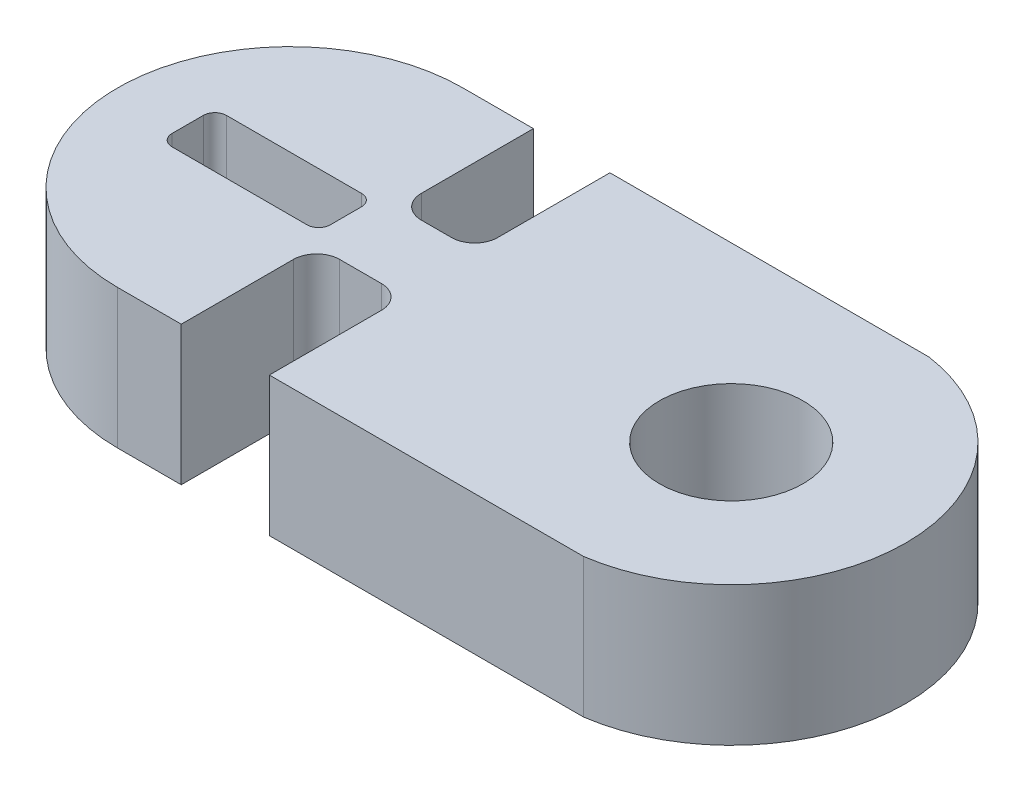
SolidWorks part; units mm, degrees
ref_plane "Alzado" through (0, 0, 0) normal (0, 0, 1) x (1, 0, 0)
ref_plane "Planta" through (0, 0, 0) normal (0, 1, 0) x (1, 0, 0)
ref_plane "Vista lateral" through (0, 0, 0) normal (1, 0, 0) x (0, 0, -1)
sketch "Croquis1" plane through (0, 0, 0) normal (0, 1, 0) x (1, 0, 0)
  line L0 (0, 0) -> (0, 15.4786) construction
  line L1 (0, 0) -> (24.3963, 0) construction
  line L2 (-10.05, 0) -> (8.9725, 0) construction
  line L3 (-10.05, 7.45) -> (-7.01, 7.45)
  line L4 (-10.05, -7.45) -> (-7.3, -7.45)
  line L5 (-17.5, 0) -> (-17.5, -13.5126) construction
  line L6 (16.5, 0) -> (16.5, -12.105) construction
  line L7 (-17.5, -13.5126) -> (-7.3, -13.5126) construction
  line L8 (-3.5, -7.45) -> (10.05, -7.45)
  line L9 (-3.71, 7.45) -> (10.05, 7.45)
  line L10 (-7.3, -7.45) -> (-7.3, -1.6141)
  line L11 (-7.3, -1.6141) -> (-3.5, -1.6141)
  line L12 (-3.5, -7.45) -> (-3.5, -1.6141)
  line L14 (-7.01, 7.45) -> (-7.01, 1.6141)
  line L15 (-7.01, 1.6141) -> (-3.71, 1.6141)
  line L16 (-3.71, 7.45) -> (-3.71, 1.6141)
  arc A0 (-10.05, 7.45) -> (-10.05, -7.45) centre (-10.05, 0) ccw
  arc A1 (10.05, -7.45) -> (10.05, 7.45) centre (8.9725, 0) ccw
  circle A2 centre (8.9725, 0) radius 3.1
  point P6 (0, 0)
  dimension "D4" = 6.2
  dimension "D1" = 14.9
  dimension "D2" = 34
  dimension "D3" = 10.2
  dimension "D5" = 3.8
extrude "Saliente-Extruir1" add sketch "Croquis1" along normal blind 6
sketch "Croquis2" plane through (0, 6, 0) normal (0, 1, 0) x (1, 0, 0)
  line L1 (-14.6227, -1.0258) -> (-7.7963, -1.0258)
  line L2 (-14.6227, -1.0258) -> (-14.6227, 1.3242)
  line L3 (-14.6227, 1.3242) -> (-7.7963, 1.3242)
  line L4 (-7.7963, -1.0258) -> (-7.7963, 1.3242)
  line L5 (-14.6227, -1.0258) -> (-7.7963, 1.3242) construction
  line L6 (-14.6227, 1.3242) -> (-7.7963, -1.0258) construction
  point P0 (-11.2095, 0.1492)
extrude "Cortar-Extruir1" cut sketch "Croquis2" against normal blind 7
fillet "Redondeo1" radius 1 4 edges at (-3.5, 3, 1.6141) (-7.3, 3, 1.6141) (-3.71, 3, -1.6141) (-7.01, 3, -1.6141)
fillet "Redondeo2" radius 0.5 4 edges at (-7.7963, 3, 1.0258) (-14.6227, 3, -1.3242) (-14.6227, 3, 1.0258) (-7.7963, 3, -1.3242)
